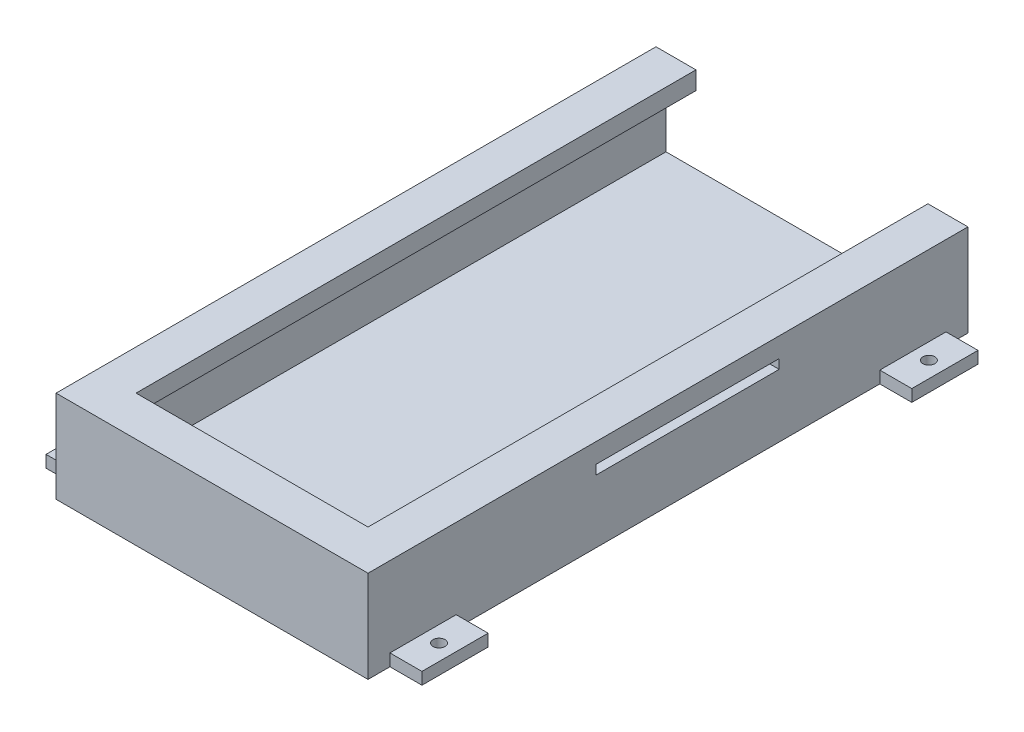
SolidWorks part; units mm, degrees
ref_plane "Front Plane" through (0, 0, 0) normal (0, 0, 1) x (1, 0, 0)
ref_plane "Top Plane" through (0, 0, 0) normal (0, 1, 0) x (1, 0, 0)
ref_plane "Right Plane" through (0, 0, 0) normal (1, 0, 0) x (0, 0, -1)
sketch "Çizim1" plane through (0, 0, 0) normal (0, 1, 0) x (1, 0, 0)
  line L1 (-30.9838, 94.802) -> (47.0162, 94.802)
  line L2 (-30.9838, 94.802) -> (-30.9838, -55.198)
  line L3 (-30.9838, -55.198) -> (47.0162, -55.198)
  line L4 (47.0162, 94.802) -> (47.0162, -55.198)
extrude "Yükseklik-Ekstrüzyon1" add sketch "Çizim1" along normal blind 18
sketch "Çizim2" plane through (0, 0, -94.802) normal (0, 0, -1) x (-1, 0, 0)
  line L0 (-47.0162, 9) -> (-44.5162, 9) construction
  line L1 (-47.0162, 18) -> (-47.0162, 0) construction
  line L2 (30.9838, 9) -> (28.4838, 9) construction
  line L3 (30.9838, 18) -> (30.9838, 0) construction
  line L4 (-40.1687, 0) -> (-40.1687, 1.5) construction
  line L5 (-47.0162, 0) -> (30.9838, 0) construction
  line L7 (-44.5162, 1.5) -> (28.4838, 1.5)
  line L8 (-44.5162, 1.5) -> (-44.5162, 18.5)
  line L9 (-44.5162, 18.5) -> (28.4838, 18.5)
  line L10 (28.4838, 1.5) -> (28.4838, 18.5)
extrude "Kes-Ekstrüzyon1" cut sketch "Çizim2" against normal blind 143 contours L8 L7 L10 L9
sketch "Çizim3" plane through (0, 18, 0) normal (0, 1, 0) x (1, 0, 0)
  line L0 (-30.9838, -55.198) -> (47.0162, -55.198) construction
  line L1 (-30.9838, -55.198) -> (47.0162, -55.198)
  line L2 (-30.9838, -55.198) -> (-30.9838, 94.802)
  line L3 (-30.9838, 94.802) -> (47.0162, 94.802)
  line L4 (47.0162, -55.198) -> (47.0162, 94.802)
  line L5 (-30.9838, 94.802) -> (-30.9838, -55.198) construction
extrude "Yükseklik-Ekstrüzyon2" add sketch "Çizim3" along normal blind 5
sketch "Çizim4" plane through (0, 0, -94.802) normal (0, 0, -1) x (-1, 0, 0)
  line L1 (-44.5162, 1.5) -> (28.4838, 1.5)
  line L2 (-44.5162, 1.5) -> (-44.5162, 18.5)
  line L3 (-44.5162, 18.5) -> (28.4838, 18.5)
  line L4 (28.4838, 1.5) -> (28.4838, 18.5)
extrude "Kes-Ekstrüzyon2" cut sketch "Çizim4" against normal blind 148
sketch "Çizim6" plane through (0, 23, 0) normal (0, 1, 0) x (1, 0, 0)
  line L0 (-30.9838, 94.802) -> (47.0162, -55.198) construction
  line L1 (47.0162, 94.802) -> (-30.9838, 94.802) construction
  line L2 (-20.9838, -45.198) -> (37.0162, -45.198)
  line L3 (-20.9838, -45.198) -> (-20.9838, 84.802)
  line L4 (-20.9838, 84.802) -> (37.0162, 84.802)
  line L5 (37.0162, -45.198) -> (37.0162, 84.802)
  line L6 (-20.9838, -45.198) -> (37.0162, 84.802) construction
  line L7 (-20.9838, 84.802) -> (37.0162, -45.198) construction
  line L8 (-20.9838, 84.802) -> (37.0162, 84.802)
  line L9 (-20.9838, 84.802) -> (-20.9838, 94.802)
  line L10 (-20.9838, 94.802) -> (37.0162, 94.802)
  line L11 (37.0162, 84.802) -> (37.0162, 94.802)
  point P4 (8.0162, 19.802)
  line M9 (47.0162, 94.802) -> (-30.9838, 94.802)
  dimension "D1" = 130
extrude "Kes-Ekstrüzyon3" cut sketch "Çizim6" against normal blind 10 contours L2 L5 L4 L3 | L4 L11 L9 M9
sketch "Çizim7" plane through (47.0162, 0, 0) normal (1, 0, 0) x (0, 0, -1)
  line L1 (1.8638, 18.0734) -> (47.6031, 18.0734)
  line L2 (1.8638, 18.0734) -> (1.8638, 15.7437)
  line L3 (1.8638, 15.7437) -> (47.6031, 15.7437)
  line L4 (47.6031, 18.0734) -> (47.6031, 15.7437)
extrude "Kes-Ekstrüzyon5" cut sketch "Çizim7" against normal blind 147
sketch "Çizim8" plane through (0, 0, 0) normal (0, -1, 0) x (1, 0, 0)
  line L0 (8.0162, 55.198) -> (8.0162, 41.4397) construction
  line L1 (-30.9838, 55.198) -> (47.0162, 55.198) construction
  line L2 (-30.9838, -19.802) -> (47.0162, -19.802) construction
  line L3 (-38.9838, 49.7162) -> (55.0162, 49.7162)
  line L4 (-38.9838, 49.7162) -> (-38.9838, 33.1632)
  line L5 (-38.9838, 33.1632) -> (55.0162, 33.1632)
  line L6 (55.0162, 49.7162) -> (55.0162, 33.1632)
  line L7 (-38.9838, 49.7162) -> (55.0162, 33.1632) construction
  line L8 (-38.9838, 33.1632) -> (55.0162, 49.7162) construction
  line L9 (-30.9838, -94.802) -> (-30.9838, 55.198) construction
  line L10 (47.0162, 55.198) -> (47.0162, -94.802) construction
  line L11 (-38.9838, -72.7672) -> (55.0162, -72.7672)
  line L12 (55.0162, -89.3201) -> (55.0162, -72.7672)
  line L13 (-38.9838, -89.3201) -> (55.0162, -89.3201)
  line L14 (-38.9838, -89.3201) -> (-38.9838, -72.7672)
extrude "Yükseklik-Ekstrüzyon4" add sketch "Çizim8" against normal blind 3
sketch "Çizim10" plane through (0, 0, -94.802) normal (0, 0, -1) x (-1, 0, 0)
  line L1 (-44.5162, 18.5) -> (28.4838, 18.5)
  line L2 (-44.5162, 18.5) -> (-44.5162, 1.5)
  line L3 (-44.5162, 1.5) -> (28.4838, 1.5)
  line L4 (28.4838, 18.5) -> (28.4838, 1.5)
extrude "Kes-Ekstrüzyon7" cut sketch "Çizim10" against normal blind 146 contours L2 L1 L4 L3
sketch "Çizim11" plane through (0, 3, 0) normal (0, 1, 0) x (1, 0, 0)
  line L0 (8.0162, -55.198) -> (8.0162, -5.5233) construction
  line L1 (-30.9838, -55.198) -> (47.0162, -55.198) construction
  line L2 (47.0162, 19.802) -> (0, 19.802) construction
  line L3 (47.0162, -55.198) -> (47.0162, 94.802) construction
  circle A0 centre (-34.9838, -41.4397) radius 1.5
  circle A1 centre (51.0162, -41.4397) radius 1.5
  circle A2 centre (51.0162, 81.0436) radius 1.5
  circle A3 centre (-34.9838, 81.0436) radius 1.5
extrude "Kes-Ekstrüzyon8" cut sketch "Çizim11" against normal blind 146
